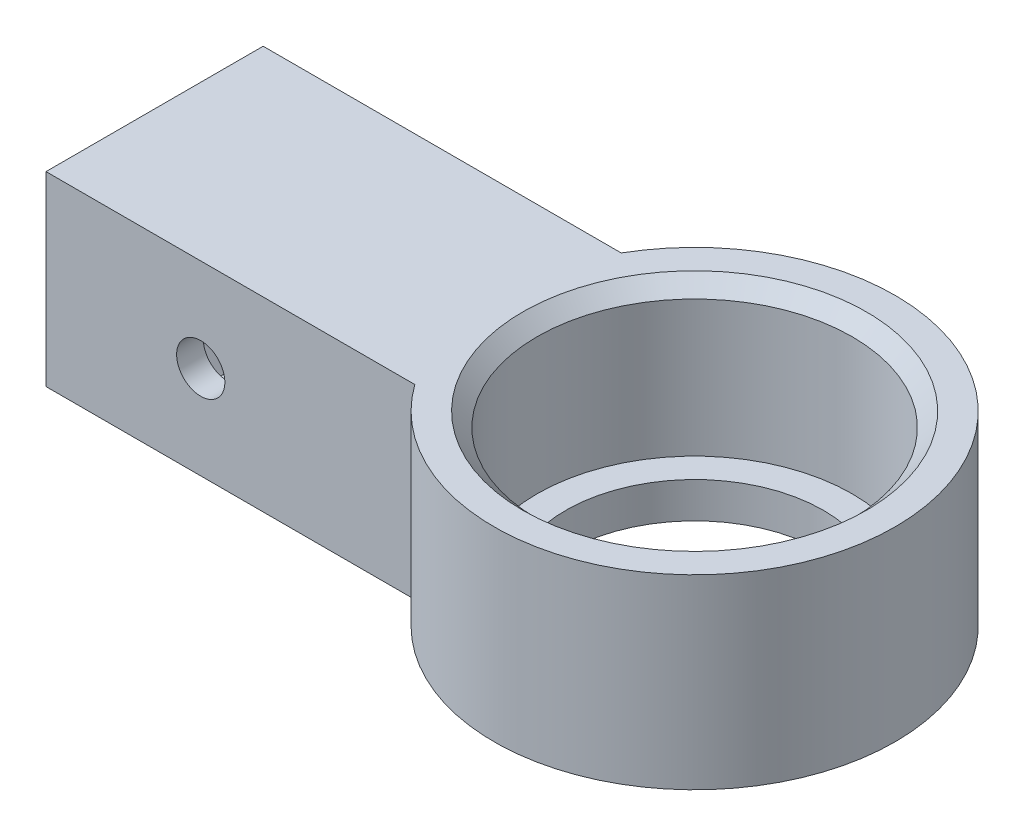
SolidWorks part; units mm, degrees
ref_plane "Plano frontal" through (0, 0, 0) normal (0, 0, 1) x (1, 0, 0)
ref_plane "Plano superior" through (0, 0, 0) normal (0, 1, 0) x (1, 0, 0)
ref_plane "Plano direito" through (0, 0, 0) normal (1, 0, 0) x (0, 0, -1)
sketch "Esboço2" plane through (0, 0, 0) normal (0, 1, 0) x (1, 0, 0)
  line L1 (-55, 0) -> (55, 0) construction
  line L4 (-12.1244, 7) -> (-37.1244, 7)
  line L5 (-37.1244, -8.161) -> (-37.1244, 7)
  line L8 (-37.1244, -8.161) -> (-11.3753, -8.161)
  circle A0 centre (0, 0) radius 11
  arc A1 (-11.3753, -8.161) -> (-12.1244, 7) centre (0, 0) ccw
  dimension "D1" = 22
  dimension "D3" = 7
  dimension "D2" = 3
  dimension "D4" = 25
extrude "Ressalto-extrusão1" add sketch "Esboço2" along normal blind 13
sketch "Esboço3" plane through (-37.1244, 0, 0) normal (-1, 0, 0) x (0, 0, 1)
  line L0 (0, -55) -> (0, 55) construction
  line L1 (3.5, 3) -> (-3.5, 3)
  line L2 (3.5, 3) -> (3.5, 10)
  line L3 (3.5, 10) -> (-3.5, 10)
  line L4 (-3.5, 3) -> (-3.5, 10)
  line L5 (3.5, 3) -> (-3.5, 10) construction
  line L6 (3.5, 10) -> (-3.5, 3) construction
  point P0 (0, 6.5)
extrude "Corte-extrusão1" cut sketch "Esboço3" against normal blind 26
sketch "Esboço7" plane through (0, 0, 3.5) normal (0, 0, -1) x (-1, 0, 0)
  line L0 (26.3212, 13) -> (26.3212, 0) construction
  line L1 (23.1458, 6.5) -> (24.7335, 3.75)
  line L2 (24.7335, 3.75) -> (27.909, 3.75)
  line L3 (27.909, 3.75) -> (29.4967, 6.5)
  line L4 (29.4967, 6.5) -> (27.909, 9.25)
  line L5 (27.909, 9.25) -> (24.7335, 9.25)
  line L6 (24.7335, 9.25) -> (23.1458, 6.5)
  line L7 (37.1244, 13) -> (11.3753, 13) construction
  line L8 (37.1244, 0) -> (11.3753, 0) construction
  circle A0 centre (26.3212, 6.5) radius 2.75 construction
  dimension "D1" = 5.5
extrude "Corte-extrusão2" cut sketch "Esboço7" against normal blind 2.8
sketch "Esboço10" plane through (0, 0, 6.3) normal (0, 0, -1) x (-1, 0, 0)
  line L0 (24.7335, 9.25) -> (27.909, 3.75) construction
  circle A0 centre (26.3212, 6.5) radius 1.6837
  point P7 (26.3212, 6.5)
extrude "Corte-extrusão3" cut sketch "Esboço10" against normal blind 2.8
sketch "Esboço11" plane through (0, 0, 0) normal (0, -1, 0) x (1, 0, 0)
  circle A0 centre (0, 0) radius 9
  circle A1 centre (0, 0) radius 11 construction
  circle A2 centre (0, 0) radius 11
  dimension "D1" = 2
extrude "Ressalto-extrusão2" add sketch "Esboço11" against normal blind 2.5
chamfer "Chanfro1" distance 1 angle 45 1 edges at (0, 13, 11)
